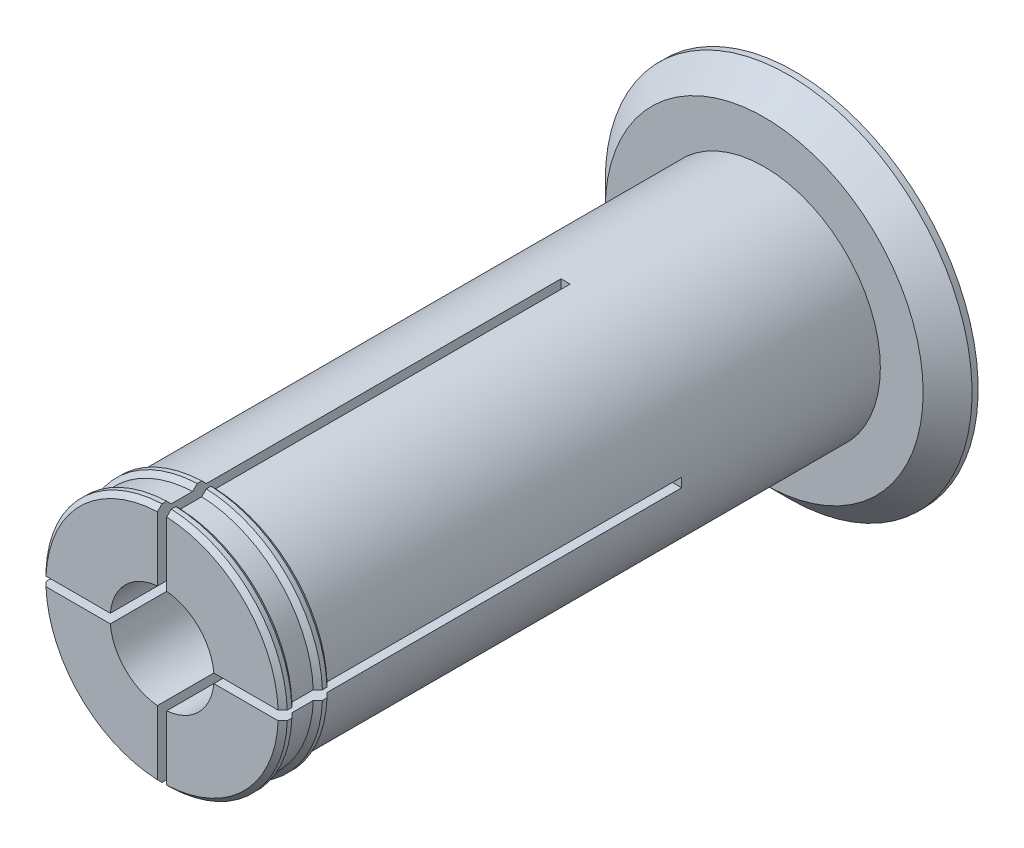
SolidWorks part; units mm, degrees
ref_plane "Front" through (0, 0, 0) normal (0, 0, 1) x (1, 0, 0)
ref_plane "Top" through (0, 0, 0) normal (0, 1, 0) x (1, 0, 0)
ref_plane "Right" through (0, 0, 0) normal (1, 0, 0) x (0, 0, -1)
sketch "Axle base sketch" plane through (0, 0, 0) normal (0, 0, 1) x (1, 0, 0)
  circle A0 centre (0, 0) radius 19
  dimension "D1" = 38
extrude "Axle" add sketch "Axle base sketch" along normal blind 98.5
sketch "Guard base" plane through (0, 0, 0) normal (0, 0, -1) x (-1, 0, 0)
  circle A0 centre (0, 0) radius 30
  dimension "D1" = 60
extrude "Guard" add sketch "Guard base" along normal blind 5
sketch "Inner axle hole base" plane through (0, 0, 98.5) normal (0, 0, 1) x (1, 0, 0)
  circle A0 centre (0, 0) radius 8.5
  dimension "D1" = 17
extrude "Inner axle hole" cut sketch "Inner axle hole base" against normal through all
sketch "Mate ring base" plane through (0, 0, 0) normal (0, 1, 0) x (1, 0, 0)
  line L0 (19, -98.5) -> (19.75, -97.75)
  line L1 (19.75, -97.75) -> (19.75, -97)
  line L2 (19.75, -97) -> (19, -96.25)
  line L3 (19.75, -97.75) -> (19.75, -98.5) construction
  line L4 (19.75, -98.5) -> (19, -98.5) construction
  line L5 (19, -96.25) -> (19, -98.5)
  line L6 (19, -98.5) -> (19, 0) construction
  line L8 (19, -92.75) -> (19.75, -92)
  line L9 (19.75, -92) -> (19.75, -91.25)
  line L10 (19.75, -91.25) -> (19, -90.5)
  line L11 (19, -90.5) -> (19, -92.75)
  dimension "D1" = 0.75
  dimension "D2" = 0.75
  dimension "D3" = 5
  dimension "D4" = 0.75
ref_axis "Center Z" through (0, 0, 0) along (0, 0, -1)
revolve "Mate rings" add sketch "Mate ring base" angle 360 about axis through (0, 0, 0) along (0, 0, -1)
sketch "Bend room base" plane through (0, 0, 98.5) normal (0, 0, 1) x (1, 0, 0)
  line L0 (0.75, -25) -> (0.75, 25)
  line L1 (0.75, 25) -> (-0.75, 25)
  line L2 (-0.75, 25) -> (-0.75, -25)
  line L3 (-0.75, -25) -> (0.75, -25)
  dimension "D1" = 0.75
  dimension "D2" = 0.75
  dimension "D3" = 25
  dimension "D4" = 25
extrude "Bend room 1" cut sketch "Bend room base" against normal blind 66
pattern_circular "Bend room 2" count 2 every 90 about axis through (0, 0, 0) along (0, 0, -1) of "Bend room 1"
chamfer "Easy removal chamfer" distance 4 angle 45 1 edges at (-30, 0, 0)
equation "\"32_92_spool_inner_diameter\"=32"
equation "\"D1@Axle base sketch\"=\"39_92_spool_inner_diameter\"- \"spool_inner_diameter_room\""
equation "\"spool_inner_diameter_room\"=1"
equation "\"32_92_spool_thickness\"=92"
equation "\"D1@Axle\"=\"39_92_spool_thickness\"+\"guard_thickness\"+\"removal_room\"*2"
equation "\"32_92_guard_diameter\"=50"
equation "\"D1@Guard base\"=\"39_92_guard_diameter\""
equation "\"guard_thickness\"=5"
equation "\"D1@Guard\"=\"guard_thickness\""
equation "\"large_inner_axle_diameter\"=20"
equation "\"D1@Inner axle hole base\"=\"small_inner_axle_diameter\""
equation "\"mate_room\"= 0.25"
equation "\"removal_room\"= 0.75"
equation "\"small_inner_axle_diameter\"=17"
equation "\"53_55_spool_inner_diameter\"=53"
equation "\"53_55_spool_thickness\"=55"
equation "\"53_55_guard_diameter\"=75"
equation "\"53_55_coupling_tooth_height\"=27"
equation "\"53_55_coupling_tooth_thickness_total\"=8"
equation "\"53_55_coupling_tooth_protrusion\"=1.5"
equation "\"53_55_coupling_tooth_head_height\"=7.5"
equation "\"53_55_coupling_tooth_depth\"=10"
equation "\"53_55_coupling_tooth_base_thickness\"=9.5"
equation "\"D1@Mate ring base\"=\"removal_room\""
equation "\"D2@Mate ring base\"=\"removal_room\""
equation "\"D3@Mate ring base\"=\"guard_thickness\""
equation "\"D4@Mate ring base\"=\"removal_room\""
equation "\"D1@Bend room base\" = \"removal_room\""
equation "\"D2@Bend room base\"=\"removal_room\""
equation "\"D3@Bend room base\"=\"32_92_guard_diameter\"/2"
equation "\"D4@Bend room base\"=\"32_92_guard_diameter\"/2"
equation "\"bend_room_length_multiplier\"=3"
equation "\"D1@Bend room 1\"=\"bend_room_length_multiplier\"*(\"39_92_spool_inner_diameter\"-\"small_inner_axle_diameter\")"
equation "\"D1@Easy removal chamfer\"=\"guard_thickness\"-1"
equation "\"32_92_extra_spool_thickness\"=-5"
equation "\"39_92_spool_inner_diameter\"=39"
equation "\"39_92_spool_thickness\"=92"
equation "\"39_92_guard_diameter\"=60"
